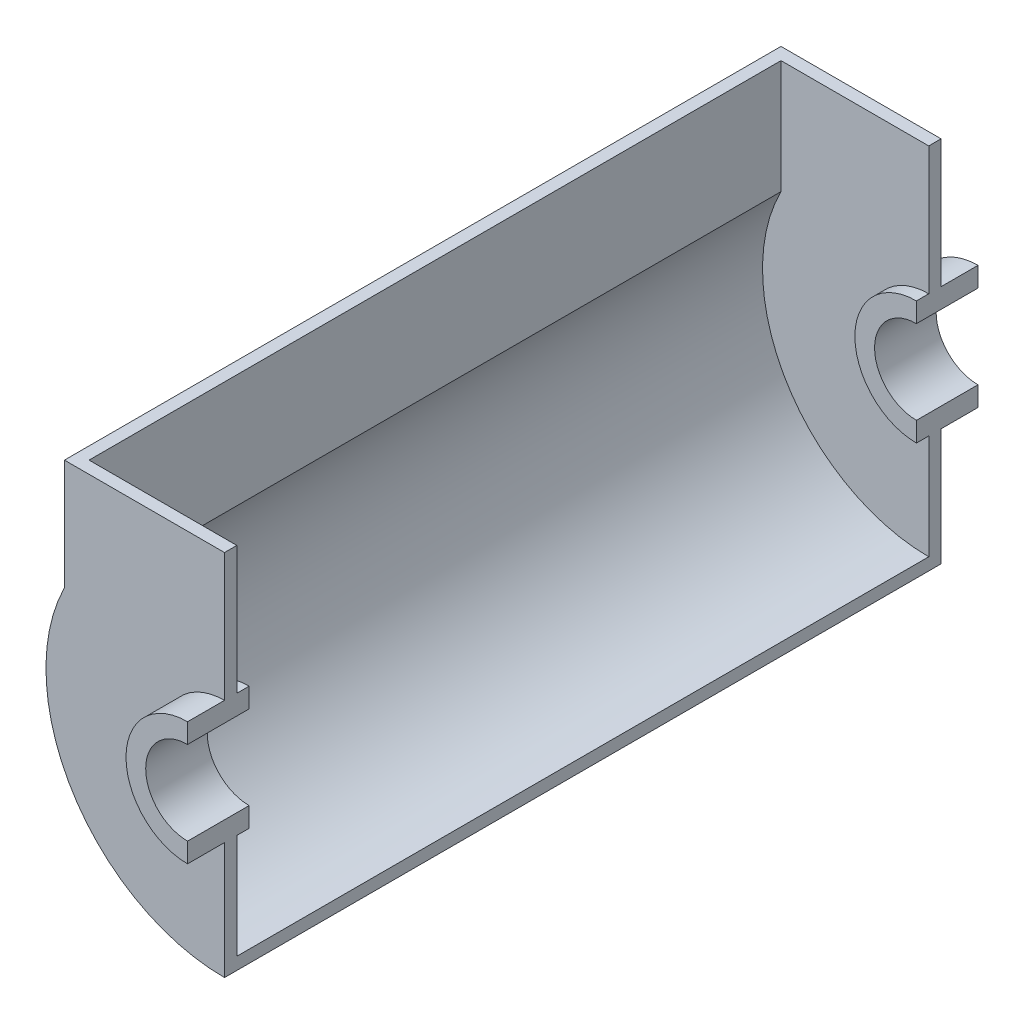
SolidWorks part; units mm, degrees
ref_plane "Front Plane" through (0, 0, 0) normal (0, 0, 1) x (1, 0, 0)
ref_plane "Top Plane" through (0, 0, 0) normal (0, 1, 0) x (1, 0, 0)
ref_plane "Right Plane" through (0, 0, 0) normal (1, 0, 0) x (0, 0, -1)
sketch "Sketch1" plane through (0, 0, 0) normal (0, 0, 1) x (1, 0, 0)
  line L0 (0, 25) -> (0, 17)
  line L1 (0, -17) -> (0, -25)
  arc A0 (0, 25) -> (0, -25) centre (0, 0) ccw
  arc A1 (0, 17) -> (0, -17) centre (0, 0) ccw
  dimension "D1" = 50
  dimension "D2" = 34
extrude "Boss-Extrude1" add sketch "Sketch1" along normal blind 20 and the other way blind 5
sketch "Sketch2" plane through (0, 0, 0) normal (0, 0, 1) x (1, 0, 0)
  line L0 (0, 25) -> (0, 77)
  line L1 (0, 77) -> (-65, 77)
  line L2 (-65, 77) -> (-65, 32.1131)
  line L3 (0, -25) -> (0, -72.5)
  arc A0 (0, 25) -> (0, -25) centre (0, 0) ccw construction
  arc A1 (0, 25) -> (0, -25) centre (0, 0) ccw
  arc A2 (-65, 32.1131) -> (0, -72.5) centre (0, 0) ccw
  dimension "D3" = 72.5
  dimension "D1" = 52
  dimension "D2" = 65
extrude "Boss-Extrude2" add sketch "Sketch2" along normal blind 5
ref_plane "Plane1" through (0, 0, -140.5) normal (0, 0, 1) x (1, 0, 0)
mirror "Mirror2" about plane through (0, 0, -140.5) normal (0, 0, 1) of bodies 102
sketch "Sketch3" plane through (0, 0, 0) normal (0, 0, -1) x (-1, 0, 0)
  line L0 (60, 30.9233) -> (60, 77)
  line L1 (0, -72.5) -> (0, -67.5)
  line L2 (65, 77) -> (60, 77)
  line L4 (0, -25) -> (0, -72.5)
  line L5 (65, 32.1131) -> (65, 77)
  line L6 (65, 77) -> (0, 77)
  line L7 (0, 77) -> (0, 25)
  line L8 (0, -25) -> (0, -72.5)
  line L9 (65, 32.1131) -> (65, 77)
  line L10 (65, 77) -> (0, 77)
  line L11 (0, 77) -> (0, 25)
  arc A0 (0, -67.5) -> (60, 30.9233) centre (0, 0) ccw
  arc A2 (0, -25) -> (0, 25) centre (0, 0) ccw
  arc A3 (0, -72.5) -> (65, 32.1131) centre (0, 0) ccw
  arc A4 (0, -25) -> (0, 25) centre (0, 0) ccw
  arc A5 (0, -72.5) -> (65, 32.1131) centre (0, 0) ccw
  dimension "D1" = 0
  dimension "D2" = 5
extrude "Boss-Extrude4" add sketch "Sketch3" along normal up to surface (281 mm away) contours A0 L1 L2 L4 L5 L0
